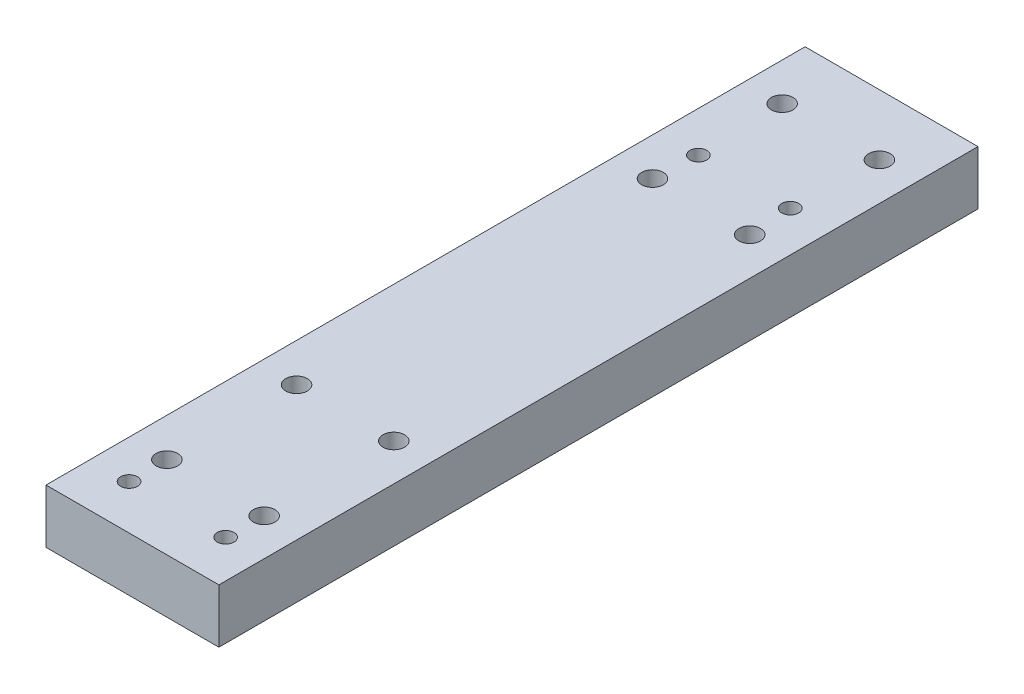
SolidWorks part; units mm, degrees
ref_plane "Front Plane" through (0, 0, 0) normal (0, 0, 1) x (1, 0, 0)
ref_plane "Top Plane" through (0, 0, 0) normal (0, 1, 0) x (1, 0, 0)
ref_plane "Right Plane" through (0, 0, 0) normal (1, 0, 0) x (0, 0, -1)
sketch "Sketch1" plane through (0, 0, 0) normal (0, 1, 0) x (1, 0, 0)
  line L1 (-16, 70.25) -> (16, 70.25)
  line L2 (-16, 70.25) -> (-16, -70.25)
  line L3 (-16, -70.25) -> (16, -70.25)
  line L4 (16, 70.25) -> (16, -70.25)
  line L5 (-16, 70.25) -> (16, -70.25) construction
  line L6 (-16, -70.25) -> (16, 70.25) construction
  circle A0 centre (-9, 59) radius 2
  circle A1 centre (9, 59) radius 2
  circle A2 centre (-9, 35) radius 2
  circle A3 centre (9, 35) radius 2
  circle A4 centre (-8.5, 43.0001) radius 1.55
  circle A5 centre (8.5, 43.0001) radius 1.55
  circle A6 centre (-8.8777, -61.9999) radius 1.55
  circle A7 centre (9, -61.9999) radius 1.55
  circle A8 centre (-8.8777, -30.9999) radius 2
  circle A9 centre (9.1223, -30.9999) radius 2
  circle A10 centre (9.1223, -54.9999) radius 2
  circle A11 centre (-8.8777, -54.9999) radius 2
  point P0 (0, 0)
  point P30 (0, 0)
  point P31 (0, 0)
  point P32 (42.4543, -4.1883)
  point P33 (0, 0)
  dimension "D3" = 4
  dimension "D4" = 4
  dimension "D5" = 4
  dimension "D6" = 4
  dimension "D14" = 3.1
  dimension "D15" = 3.1
  dimension "D16" = 3.1
  dimension "D17" = 3.1
  dimension "D20" = 4
  dimension "D21" = 4
  dimension "D22" = 4
  dimension "D23" = 4
  dimension "D1" = 32
  dimension "D2" = 140.5
  dimension "D7" = 18
  dimension "D8" = 24
  dimension "D9" = 18
  dimension "D10" = 9
  dimension "D11" = 35
  dimension "D12" = 17
  dimension "D13" = 8.5
  dimension "D18" = 105
  dimension "D19" = 105
  dimension "D24" = 18
  dimension "D25" = 24
  dimension "D26" = 24
  dimension "D27" = 24
  dimension "D28" = 7
  dimension "D29" = 35
extrude "Boss-Extrude1" add sketch "Sketch1" along normal blind 10
